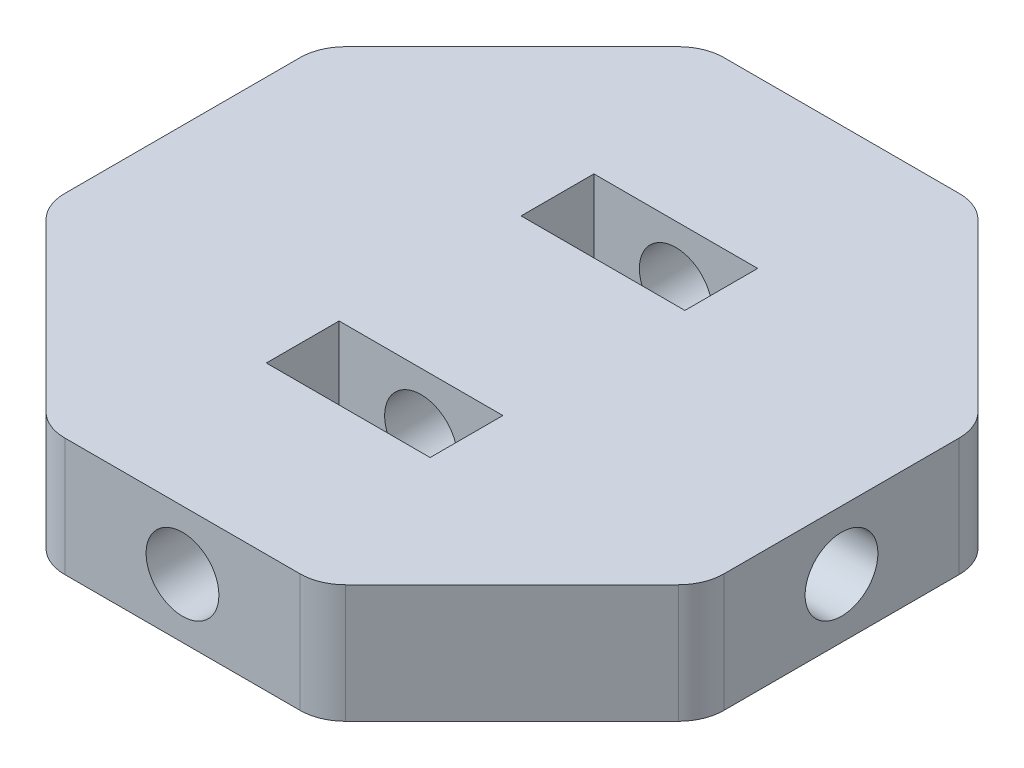
SolidWorks part; units mm, degrees
ref_plane "Front Plane" through (0, 0, 0) normal (0, 0, 1) x (1, 0, 0)
ref_plane "Top Plane" through (0, 0, 0) normal (0, 1, 0) x (1, 0, 0)
ref_plane "Right Plane" through (0, 0, 0) normal (1, 0, 0) x (0, 0, -1)
sketch "Sketch1" plane through (0, 0, 0) normal (0, 1, 0) x (1, 0, 0)
  line L0 (15, -36.2132) -> (36.2132, -15)
  line L1 (36.2132, -15) -> (36.2132, 15)
  line L2 (36.2132, 15) -> (15, 36.2132)
  line L3 (15, 36.2132) -> (-15, 36.2132)
  line L5 (-15, 36.2132) -> (-36.2132, 15)
  line L6 (-36.2132, 15) -> (-36.2132, -15)
  line L7 (-36.2132, -15) -> (-15, -36.2132)
  line L8 (-15, -36.2132) -> (15, -36.2132)
extrude "Extrude2" add sketch "Sketch1" along normal blind 13
sketch "Sketch2" plane through (36.2132, 0, 0) normal (1, 0, 0) x (0, 0, -1)
  circle A0 centre (0, 6.5) radius 4
extrude "Extrude3" cut sketch "Sketch2" against normal up to next
sketch "Sketch3" plane through (0, 0, 36.2132) normal (0, 0, 1) x (1, 0, 0)
  circle A0 centre (0, 6.5) radius 4
extrude "Extrude4" cut sketch "Sketch3" against normal through all
sketch "Sketch4" plane through (0, 13, 0) normal (0, 1, 0) x (1, 0, 0)
  line L1 (-9, -10) -> (9, -10)
  line L2 (-9, -10) -> (-9, -18)
  line L3 (-9, -18) -> (9, -18)
  line L4 (9, -10) -> (9, -18)
  line L5 (-9, 10) -> (9, 10)
  line L6 (-9, 10) -> (-9, 18)
  line L7 (-9, 18) -> (9, 18)
  line L8 (9, 10) -> (9, 18)
extrude "Extrude5" cut sketch "Sketch4" against normal blind 13
fillet "Fillet1" radius 5 8 edges at (15, 6.5, -36.2132) (36.2132, 6.5, -15) (36.2132, 6.5, 15) (15, 6.5, 36.2132) (-15, 6.5, 36.2132) (-36.2132, 6.5, 15) (-36.2132, 6.5, -15) (-15, 6.5, -36.2132)
